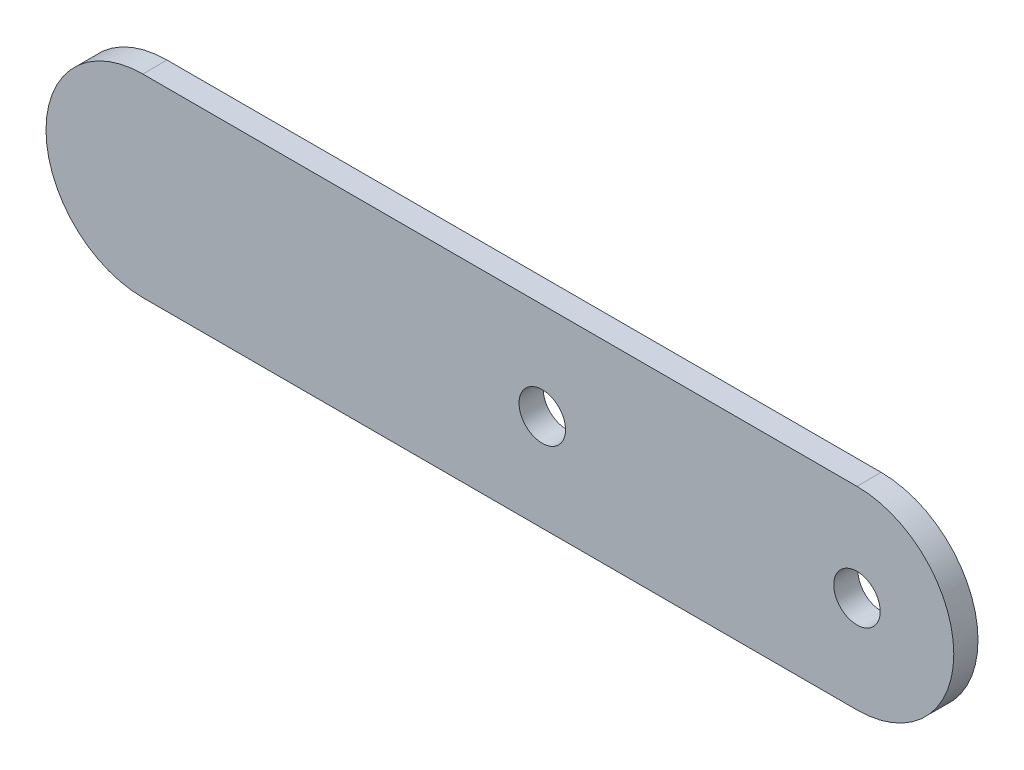
SolidWorks part; units mm, degrees
ref_plane "Front" through (0, 0, 0) normal (0, 0, 1) x (1, 0, 0)
ref_plane "Top" through (0, 0, 0) normal (0, 1, 0) x (1, 0, 0)
ref_plane "Right" through (0, 0, 0) normal (1, 0, 0) x (0, 0, -1)
sketch "Sketch1" plane through (0, 0, 0) normal (0, 0, 1) x (1, 0, 0)
  line L1 (-46.8312, -12.7) -> (46.8313, -12.7)
  line L2 (-46.8312, -12.7) -> (-46.8312, 12.7) construction
  line L3 (-46.8312, 12.7) -> (46.8313, 12.7)
  line L4 (46.8313, -12.7) -> (46.8313, 12.7) construction
  line L5 (-46.8312, -12.7) -> (46.8313, 12.7) construction
  line L6 (-46.8312, 12.7) -> (46.8313, -12.7) construction
  arc A0 (-46.8312, 12.7) -> (-46.8312, -12.7) centre (-46.8312, 0) ccw
  arc A1 (46.8313, -12.7) -> (46.8313, 12.7) centre (46.8313, 0) ccw
  circle A2 centre (46.8313, 0) radius 3.048
  circle A3 centre (5.5563, 0) radius 3.048
  point P0 (0, 0)
  dimension "D4" = 6.096
  dimension "D5" = 6.096
  dimension "D1" = 25.4
  dimension "D2" = 93.6625
  dimension "D3" = 41.275
extrude "Boss-Extrude1" add sketch "Sketch1" along normal blind 3.175
